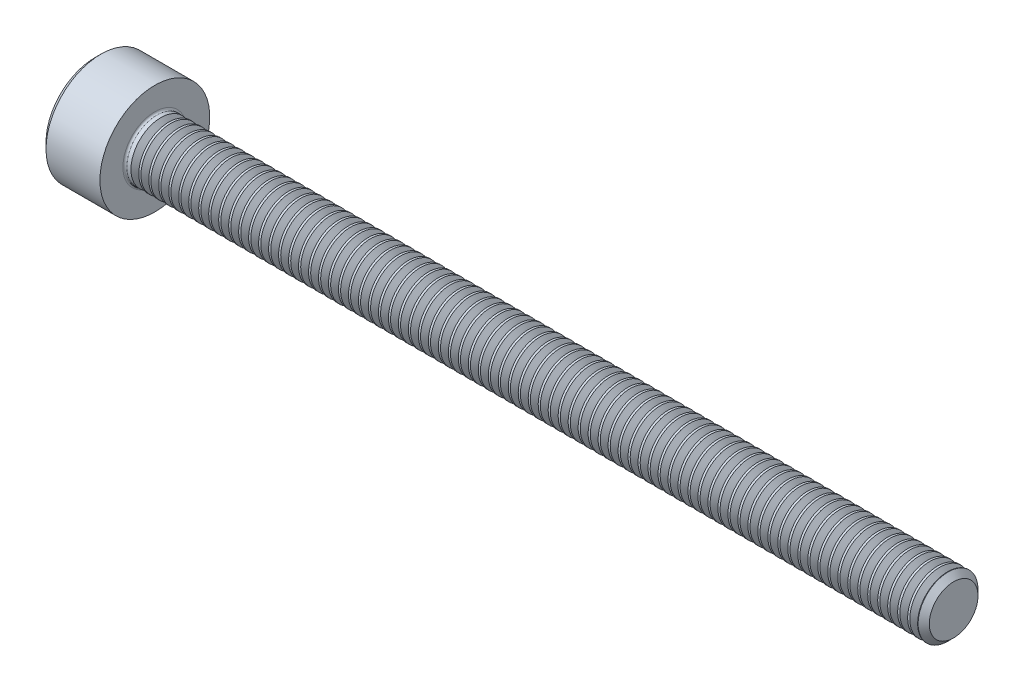
SolidWorks part; units mm, degrees
revolve "Base-Revolve" add sketch "BodySke"
sketch "BodySke" plane through (0, 0, 0) normal (0, 0, 1) x (1, 0, 0)
  line L0 (0, 0) -> (0, 2.45)
  line L1 (0.3, 2.75) -> (3, 2.75)
  line L2 (3, 2.75) -> (3, 1.5)
  line L3 (3, 1.5) -> (42.7195, 1.5)
  line L4 (43, 1.2195) -> (43, 0)
  line L5 (43, 0) -> (0, 0)
  line L6 (-31.75, 0) -> (127, 0) construction
  line L7 (0, 2.45) -> (0.3, 2.75)
  line L8 (43, 1.2195) -> (42.7195, 1.5)
  line L9 (0, -2.45) -> (0.3, -2.75) construction
  line L10 (43, -1.2195) -> (42.7195, -1.5) construction
  line L11 (3.5, 9.525) -> (3.5, 3.175) construction
  line L12 (3, 9.525) -> (3, 3.175) construction
  line L13 (-7, 9.525) -> (-7, 3.175) construction
  dimension "Diameter" = 3
  dimension "Head_ht" = 3
  dimension "Length" = 40
  dimension "Body_ch_ang" = 45
  dimension "Head_dia" = 5.5
  dimension "Head_ch_ang" = 45
  dimension "Minor_dia" = 2.439
  dimension "Advance" = 0.5
  dimension "Thread_nom" = 40
  dimension "Thread_length" = 50
  dimension "Head_ch_ht" = 0.3
cosmetic thread "ThreadCosmetic" [suppressed]
fillet "Fillet1" radius 0.1 1 edges at (3, 0, 1.5)
ref_plane "Plane1" through (0, 0, 0) normal (0, 0, 1) x (1, 0, 0)
ref_plane "Plane2" through (0, 0, 0) normal (0, 1, 0) x (1, 0, 0)
ref_plane "Plane3" through (0, 0, 0) normal (1, 0, 0) x (0, 0, -1)
sketch "Sketch2" plane through (0, 0, 0) normal (0, 0, 1) x (1, 0, 0)
  line L0 (0, 1.28) -> (1.3, 1.28)
  line L1 (1.3, 1.28) -> (2.039, 0)
  line L2 (-31.75, 0) -> (127, 0) construction
  line L3 (2.039, 0) -> (0, 0)
  line L4 (0, 0) -> (0, 1.28)
  line L5 (0, 2.45) -> (0, -2.45) construction
  line L6 (0, 0) -> (47.625, 0) construction
  line L7 (3, -2.75) -> (3, 2.75) construction
  dimension "D1" = 1.28
  dimension "D2" = 60
revolve "Hex-PreBroach" cut sketch "Sketch2" angle 360 about L6
sketch "Sketch3" plane through (0, 0, 0) normal (-1, 0, 0) x (0, 0.5, 0.866)
  line L0 (0.739, 1.28) -> (-0.739, 1.28)
  line L1 (-0.739, 1.28) -> (-1.478, 0)
  line L2 (0.739, 1.28) -> (1.478, 0)
  line L3 (0.739, -1.28) -> (1.478, 0)
  line L4 (0.739, -1.28) -> (-0.739, -1.28)
  line L5 (-0.739, -1.28) -> (-1.478, 0)
  dimension "D1" = 1.28
  dimension "D2" = 1.28
  dimension "Hex_size" = 2.56
extrude "Hex" cut sketch "Sketch3" against normal blind 1.3
sketch "Sketch4" plane through (0, 0, 0) normal (-1, 0, 0) x (0, 0, 1)
  line L0 (0, 0) -> (1.4605, 0)
  line L1 (0, 0) -> (6.1484, 3.5498) construction
  line L2 (0, 0) -> (0.7302, 1.2648)
  line L3 (1.2009, 0.3267) -> (1.3933, 0.4378)
  line L4 (0.8834, 0.8767) -> (1.0758, 0.9877)
  arc A0 (1.2009, 0.3267) -> (0.8834, 0.8767) centre (0, 0) ccw
  arc A1 (1.4605, 0) -> (1.3933, 0.4378) centre (0, 0) ccw
  arc A2 (0.7302, 1.2648) -> (1.0758, 0.9877) centre (0, 0) cw
  dimension "D1" = 30
  dimension "D2" = 60
  dimension "Spline_p_dim" = 0.635
  dimension "D3" = 0.3175
extrude "Spline" [suppressed] cut sketch "Sketch4" against normal blind 1.3
pattern_circular "CirPattern1" [suppressed] count 6 every 60
sketch "Sketch5" plane through (0, 0, 0) normal (0, 0, 1) x (1, 0, 0)
  line L0 (-31.75, 0) -> (127, 0) construction
  line L2 (0, 2.45) -> (0, -2.45) construction
  circle A0 centre (1.2, 0) radius 0.475
  dimension "Drilled_hole_dia" = 0.95
  dimension "Drilled_hole_loc" = 1.2
extrude "Hole" [suppressed] cut sketch "Sketch5" against normal through all and the other way through all
pattern_circular "Drilled-4" [suppressed] count 2 every 60
pattern_circular "Drilled-6" [suppressed] count 3 every 60
sketch "ThdSchSke" plane through (0, 0, 0) normal (0, 0, 1) x (1, 0, 0)
  line L0 (3.5, -1.2195) -> (3.3036, -1.5)
  line L1 (3.5, -1.2195) -> (3.6964, -1.5)
  line L2 (3.6964, -1.5) -> (3.6964, -1.875)
  line L3 (-3.175, 0) -> (5.1513, 0) construction
  line L5 (3.6964, -1.875) -> (3.3036, -1.875)
  line L6 (3.3036, -1.875) -> (3.3036, -1.5)
  line L7 (0, 2.45) -> (0, -2.45) construction
  dimension "Thread_minor" = 2.439
  dimension "Diameter" = 3
  dimension "Start" = 3.5
revolve "ThreadSchematic" cut sketch "ThdSchSke" angle 360 about L3
pattern_linear "ThdSchPat" count 79 spacing 0.5 along (1, 0, 0) of "ThreadSchematic"
equation "\"D2@Sketch3\" = \"Hex_size@Sketch3\" / 2"
equation "\"D1@Sketch3\" = \"Hex_size@Sketch3\" / 2"
equation "\"D1@Sketch2\" = \"Hex_size@Sketch3\" / 2"
equation "\"D3@Sketch4\" = \"Spline_p_dim@Sketch4\" / 2"
equation "\"Thread_minor@ThreadCosmetic\"  =  \"Minor_dia@BodySke\""
equation "\"D2@CirPattern1\" = 360 / \"Num_teeth@CirPattern1\""
equation "\"Wall_thickness@Sketch2\" = \"Head_ht@BodySke\" - \"Key_eng@Hex\""
equation "\"Thread_length@ThreadCosmetic\" = ((sgn( (\"Length@BodySke\" - \"Advance@BodySke\" ) - \"Thread_nom@BodySke\" )-1)*( (\"Length@BodySke\" - \"Advance@BodySke\" ) - \"Thread_nom@BodySke\" ))/-2+ \"Thread_nom@BodySke\""
equation "\"Thread_minor@ThdSchSke\" = \"Minor_dia@BodySke\""
equation "\"Diameter@ThdSchSke\" = \"Diameter@BodySke\""
equation "\"Overcut@ThdSchSke\" = \"Diameter@BodySke\" * 1.25"
equation "\"Start@ThdSchSke\" = \"Head_ht@BodySke\" + \"Length@BodySke\" - \"Thread_length@ThreadCosmetic\"  '---Non-countersunk---"
equation "\"Num_threads@ThdSchPat\" = int( \"Thread_length@ThreadCosmetic\" / \"Advance@BodySke\" + 0.999 )  + 1"
equation "\"Advance@ThdSchPat\" = \"Thread_length@ThreadCosmetic\" /  (\"Num_threads@ThdSchPat\" - 1) 'relax it"
equation "\"Num_threads@ThdSchPat\" = \"Num_threads@ThdSchPat\" - sgn( \"Num_threads@ThdSchPat\" - 1) '---chamfered tips only---"
